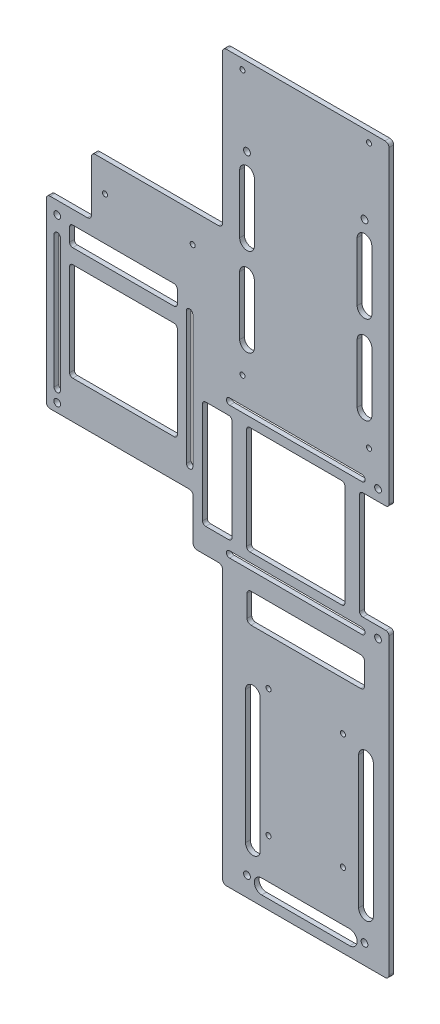
SolidWorks part; units mm, degrees
material "Acrylic (Medium-high impact)"
ref_plane "Front Plane" through (0, 0, 0) normal (0, 0, 1) x (1, 0, 0)
ref_plane "Top Plane" through (0, 0, 0) normal (0, 1, 0) x (1, 0, 0)
ref_plane "Right Plane" through (0, 0, 0) normal (1, 0, 0) x (0, 0, -1)
sketch "Sketch1" plane through (0, 0, 0) normal (0, 0, 1) x (1, 0, 0)
  line L1 (-159.4912, -174.7551) -> (-51.5412, -174.7551)
  line L2 (-159.4912, -174.7551) -> (-159.4912, 295.1449)
  line L3 (-159.4912, 295.1449) -> (-51.5412, 295.1449)
  line L4 (-51.5412, -174.7551) -> (-51.5412, 295.1449)
  line L5 (-159.4912, -174.7551) -> (-51.5412, 295.1449) construction
  line L6 (-159.4912, 295.1449) -> (-51.5412, -174.7551) construction
  point P0 (-105.5162, 60.1949)
  dimension "D1" = 107.95
  dimension "D2" = 469.9
extrude "Boss-Extrude1" add sketch "Sketch1" along normal blind 3.0734
sketch "Sketch2" plane through (0, 0, 3.0734) normal (0, 0, 1) x (1, 0, 0)
  line L0 (-134.0912, -163.6426) -> (-76.9412, -163.6426) construction
  line L1 (-134.0912, -158.8801) -> (-76.9412, -158.8801)
  line L2 (-134.0912, -168.4051) -> (-76.9412, -168.4051)
  line L3 (-105.5162, 295.1449) -> (-105.5162, -174.7551) construction
  line L4 (-159.4912, 295.1449) -> (-159.4912, -174.7551) construction
  line L5 (-51.5412, -174.7551) -> (-51.5412, 295.1449) construction
  line L6 (-51.5412, 295.1449) -> (-159.4912, 295.1449) construction
  line L7 (-159.4912, -174.7551) -> (-51.5412, -174.7551) construction
  line L8 (-66.4637, -58.2591) -> (-66.4637, -144.2751) construction
  line L9 (-61.7012, -58.2591) -> (-61.7012, -144.2751)
  line L10 (-71.2262, -58.2591) -> (-71.2262, -144.2751)
  line L11 (-139.8062, -58.2591) -> (-139.8062, -144.2751) construction
  line L13 (-68.7497, -58.2591) -> (-67.4797, -58.2591) construction
  line L14 (-144.5687, -58.2591) -> (-144.5687, -144.2751)
  line L15 (-135.0437, -58.2591) -> (-135.0437, -144.2751)
  line L16 (-139.8062, -144.2751) -> (-105.5162, -144.2751) construction
  line L17 (-105.5162, -144.2751) -> (-71.2262, -144.2751) construction
  arc A0 (-134.0912, -158.8801) -> (-134.0912, -168.4051) centre (-134.0912, -163.6426) ccw
  arc A1 (-76.9412, -168.4051) -> (-76.9412, -158.8801) centre (-76.9412, -163.6426) ccw
  arc A2 (-61.7012, -58.2591) -> (-71.2262, -58.2591) centre (-66.4637, -58.2591) ccw
  arc A3 (-71.2262, -144.2751) -> (-61.7012, -144.2751) centre (-66.4637, -144.2751) ccw
  arc A4 (-144.5687, -58.2591) -> (-135.0437, -58.2591) centre (-139.8062, -58.2591) cw
  arc A5 (-135.0437, -144.2751) -> (-144.5687, -144.2751) centre (-139.8062, -144.2751) cw
  point P2 (-105.5162, -163.6426)
  point P15 (-66.4637, -101.2671)
  point P30 (-139.8062, -101.2671)
  dimension "D1" = 6.35
  dimension "D2" = 25.4
  dimension "D3" = 25.4
  dimension "D4" = 10.16
  dimension "D5" = 0
  dimension "D6" = 9.525
  dimension "D7" = 30.48
  dimension "D8" = 9.525
extrude "Arudino Wire Slots" cut sketch "Sketch2" against normal up to next
sketch "Sketch6" plane through (0, 0, 3.0734) normal (0, 0, 1) x (1, 0, 0)
  line L3 (-51.5412, 295.1449) -> (-159.4912, 295.1449) construction
  line L4 (-51.5412, -174.7551) -> (-51.5412, 295.1449) construction
  line L13 (-67.4162, 231.6449) -> (-67.4162, 193.5449) construction
  line L14 (-62.6537, 231.6449) -> (-62.6537, 193.5449)
  line L15 (-72.1787, 231.6449) -> (-72.1787, 193.5449)
  arc A2 (-62.6537, 231.6449) -> (-72.1787, 231.6449) centre (-67.4162, 231.6449) ccw
  arc A3 (-72.1787, 193.5449) -> (-62.6537, 193.5449) centre (-67.4162, 193.5449) ccw
  point P23 (-67.4162, 212.5949)
  dimension "D1" = 15.875
  dimension "D2" = 63.5
  dimension "D3" = 9.525
  dimension "D4" = 38.1
extrude "PowerBoardWirePass" cut sketch "Sketch6" against normal up to next (3.0734 mm away)
pattern_linear "LPattern2" count 2 spacing 57.15 along (0, -1, 0) count 2 spacing 76.2 along (-1, 0, 0) of "PowerBoardWirePass"
sketch "Sketch8" plane through (0, 0, 3.0734) normal (0, 0, 1) x (1, 0, 0)
  line L0 (-159.4912, -10.8302) -> (-51.5412, -10.8302) construction
  line L1 (-159.4912, 295.1449) -> (-159.4912, -174.7551) construction
  line L2 (-51.5412, -174.7551) -> (-51.5412, 295.1449) construction
  line L4 (-143.6162, -20.3552) -> (-67.4162, -20.3552)
  line L5 (-143.6162, -20.3552) -> (-143.6162, -1.3052)
  line L6 (-143.6162, -1.3052) -> (-67.4162, -1.3052)
  line L7 (-67.4162, -20.3552) -> (-67.4162, -1.3052)
  line L8 (-143.6162, -20.3552) -> (-67.4162, -1.3052) construction
  line L9 (-143.6162, -1.3052) -> (-67.4162, -20.3552) construction
  point P6 (-105.5162, -10.8302)
  dimension "D1" = 19.05
  dimension "D2" = 76.2
extrude "Cut-Extrude5" cut sketch "Sketch8" against normal through all
hole_wizard "#30 (0.1285) Arduino Mounts" positions "Sketch14" profile "Sketch15" hole size "#30" standard "ANSI Inch" end condition through all
sketch "Sketch14" plane through (0, 0, 3.0734) normal (0, 0, 1) x (1, 0, 0)
  line L0 (-159.4912, -174.7551) -> (-51.5412, -174.7551) construction
  line L3 (-105.5162, -34.436) -> (-105.5162, -174.7551) construction
  point P0 (-129.6462, -50.2951)
  point P2 (-129.6462, -132.8451)
  point P4 (-81.3862, -51.5651)
  point P6 (-81.3862, -126.4951)
  dimension "D1" = 48.26
  dimension "D2" = 82.55
  dimension "D3" = 74.93
  dimension "D4" = 41.91
  dimension "D5" = 1.27
  dimension "D6" = 24.13
sketch "Sketch15" plane through (-129.6462, -50.2951, 3.0734) normal (1, 0, 0) x (0, -1, 0)
  line L0 (0, 0) -> (0, 3.0734)
  line L1 (0, 3.0734) -> (1.6319, 3.0734)
  line L2 (1.6319, 3.0734) -> (1.6319, 0)
  line L5 (1.6319, 0) -> (0, 0)
  line L11 (0, -6.35) -> (0, 107.95) construction
  dimension "Thru Hole Dia." = 3.2639
  dimension "Thru Hole Depth" = 3.0734
sketch "Sketch18" plane through (0, 0, 0) normal (0, 0, 1) x (1, 0, 0)
  line L0 (-159.4912, 193.5449) -> (-273.7912, 193.5449)
  line L1 (-159.4912, 295.1449) -> (-159.4912, -174.7551) construction
  line L2 (-273.7912, 193.5449) -> (-273.7912, 36.0649)
  line L3 (-273.7912, 36.0649) -> (-178.5412, 36.0649)
  line L4 (-159.4912, 193.5449) -> (-159.4912, 4.3149)
  line L5 (-51.5412, 295.1449) -> (-159.4912, 295.1449) construction
  line L6 (-178.5412, 36.0649) -> (-178.5412, 4.3149)
  line L7 (-178.5412, 4.3149) -> (-159.4912, 4.3149)
  line L8 (-159.4912, 295.1449) -> (-159.4912, -174.7551) construction
  dimension "D1" = 259.08
  dimension "D2" = 114.3
  dimension "D3" = 101.6
  dimension "D4" = 19.05
  dimension "D5" = 31.75
extrude "Boss-Extrude2" add sketch "Sketch18" along normal blind 3.0734
hole_wizard "#30 (0.1285) Diameter Hole1" positions "Sketch12" profile "Sketch13" hole size "#30" standard "ANSI Inch" end condition through all
sketch "Sketch12" plane through (0, 0, 3.0734) normal (0, 0, 1) x (1, 0, 0)
  line L0 (-146.5372, 117.3449) -> (-146.5372, 288.7949) construction
  line L1 (-146.5372, 288.7949) -> (-64.4952, 288.7949) construction
  line L2 (-64.4952, 288.7949) -> (-64.4952, 117.3449) construction
  line L3 (-64.4952, 117.3449) -> (-146.5372, 117.3449) construction
  line L5 (-51.5412, 295.1449) -> (-159.4912, 295.1449) construction
  line L7 (-105.5162, 295.1449) -> (-105.5162, 288.7949) construction
  line L8 (-159.4912, 193.5449) -> (-273.7912, 193.5449) construction
  line L9 (-273.7912, 193.5449) -> (-273.7912, 36.0649) construction
  point P0 (-64.4952, 288.7949)
  point P2 (-146.5372, 288.7949)
  point P4 (-146.5372, 117.3449)
  point P6 (-64.4952, 117.3449)
  point P26 (-235.6912, 174.4949)
  point P28 (-178.8714, 174.4949)
  dimension "D1" = 82.042
  dimension "D2" = 171.45
  dimension "D3" = 6.35
  dimension "D4" = 19.05
  dimension "D5" = 38.1
  dimension "D6" = 56.8198
sketch "Sketch13" plane through (-64.4952, 288.7949, 3.0734) normal (1, 0, 0) x (0, -1, 0)
  line L0 (0, 0) -> (0, 3.0734)
  line L1 (0, 3.0734) -> (1.6319, 3.0734)
  line L2 (1.6319, 3.0734) -> (1.6319, 0)
  line L5 (1.6319, 0) -> (0, 0)
  line L11 (0, -6.35) -> (0, 107.95) construction
  dimension "Thru Hole Dia." = 3.2639
  dimension "Thru Hole Depth" = 3.0734
sketch "Sketch19" plane through (0, 0, 3.0734) normal (0, 0, 1) x (1, 0, 0)
  line L0 (-153.3952, 88.2386) -> (-153.3952, 22.4886)
  line L1 (-162.9202, 75.7358) -> (-162.9202, 39.7972) construction
  line L2 (-172.4452, 88.2386) -> (-172.4452, 22.4886)
  line L3 (-170.3952, 90.2886) -> (-155.4452, 90.2886)
  line L4 (-426.1023, 140.2049) -> (-409.9638, 140.2049) construction
  line L5 (-256.6409, 146.5549) -> (-190.8909, 146.5549)
  line L6 (-170.3952, 20.4386) -> (-155.4452, 20.4386)
  line L7 (-223.7659, 60.5759) -> (-223.7659, 124.3299) construction
  line L9 (-51.5412, 295.1449) -> (-159.4912, 295.1449) construction
  line L12 (-266.6972, 49.5269) -> (-266.6972, 135.3789) construction
  line L13 (-268.7472, 49.5269) -> (-268.7472, 135.3789)
  line L14 (-51.5412, -174.7551) -> (-51.5412, 295.1449) construction
  line L15 (-154.9192, 98.2949) -> (-69.0672, 98.2949) construction
  line L16 (-154.9192, 100.3449) -> (-69.0672, 100.3449)
  line L17 (-154.9192, 96.2449) -> (-69.0672, 96.2449)
  line L18 (-53.5912, 90.2886) -> (-68.5412, 90.2886)
  line L19 (-70.5912, 88.2386) -> (-70.5912, 22.4886)
  line L20 (-68.5412, 20.4386) -> (-53.5912, 20.4386)
  line L21 (-51.5412, 92.3386) -> (-51.5412, 18.3886)
  line L22 (-264.6472, 49.5269) -> (-264.6472, 135.3789)
  line L23 (-154.3518, 55.3689) -> (-93.9593, 55.3689) construction
  line L24 (-154.9192, 12.4429) -> (-69.0672, 12.4429) construction
  line L25 (-154.9192, 10.3929) -> (-69.0672, 10.3929)
  line L26 (-154.9192, 14.4929) -> (-69.0672, 14.4929)
  line L27 (-75.3537, 88.6756) -> (-75.3537, 77.0683) construction
  line L28 (-80.1162, 88.2386) -> (-80.1162, 22.4886)
  line L29 (-111.9932, 87.7921) -> (-111.9932, 31.1048) construction
  line L30 (-143.8702, 88.2386) -> (-143.8702, 22.4886)
  line L31 (-141.8202, 90.2886) -> (-82.1662, 90.2886)
  line L32 (-258.6909, 135.9049) -> (-258.6909, 144.5049)
  line L33 (-82.1662, 20.4386) -> (-141.8202, 20.4386)
  line L34 (-256.6409, 133.8549) -> (-190.8909, 133.8549)
  line L35 (-188.8409, 135.9049) -> (-188.8409, 144.5049)
  line L38 (-180.8452, 49.5269) -> (-180.8452, 135.3789) construction
  line L39 (-178.7952, 49.5269) -> (-178.7952, 135.3789)
  line L40 (-182.8952, 49.5269) -> (-182.8952, 135.3789)
  line L41 (-454.9809, 129.0924) -> (-443.3736, 129.0924) construction
  line L42 (-256.6409, 124.3299) -> (-190.8909, 124.3299)
  line L43 (-258.6909, 92.4529) -> (-188.8515, 92.4529) construction
  line L44 (-256.6409, 60.5759) -> (-190.8909, 60.5759)
  line L45 (-258.6909, 62.6259) -> (-258.6909, 122.2799)
  line L46 (-188.8409, 122.2799) -> (-188.8409, 62.6259)
  arc A0 (-51.5412, 92.3386) -> (-53.5912, 90.2886) centre (-53.5912, 92.3386) cw
  arc A1 (-154.9192, 100.3449) -> (-154.9192, 96.2449) centre (-154.9192, 98.2949) ccw
  arc A2 (-69.0672, 96.2449) -> (-69.0672, 100.3449) centre (-69.0672, 98.2949) ccw
  arc A3 (-53.5912, 20.4386) -> (-51.5412, 18.3886) centre (-53.5912, 18.3886) cw
  arc A4 (-68.5412, 90.2886) -> (-70.5912, 88.2386) centre (-68.5412, 88.2386) ccw
  arc A5 (-70.5912, 22.4886) -> (-68.5412, 20.4386) centre (-68.5412, 22.4886) ccw
  circle A6 centre (-64.4952, 117.3449) radius 1.6319 construction
  arc A7 (-154.9192, 10.3929) -> (-154.9192, 14.4929) centre (-154.9192, 12.4429) cw
  arc A8 (-69.0672, 14.4929) -> (-69.0672, 10.3929) centre (-69.0672, 12.4429) cw
  arc A9 (-80.1162, 22.4886) -> (-82.1662, 20.4386) centre (-82.1662, 22.4886) cw
  arc A10 (-82.1662, 90.2886) -> (-80.1162, 88.2386) centre (-82.1662, 88.2386) cw
  arc A11 (-143.8702, 22.4886) -> (-141.8202, 20.4386) centre (-141.8202, 22.4886) ccw
  arc A12 (-141.8202, 90.2886) -> (-143.8702, 88.2386) centre (-141.8202, 88.2386) ccw
  arc A13 (-153.3952, 22.4886) -> (-155.4452, 20.4386) centre (-155.4452, 22.4886) cw
  arc A14 (-155.4452, 90.2886) -> (-153.3952, 88.2386) centre (-155.4452, 88.2386) cw
  arc A15 (-172.4452, 22.4886) -> (-170.3952, 20.4386) centre (-170.3952, 22.4886) ccw
  arc A16 (-170.3952, 90.2886) -> (-172.4452, 88.2386) centre (-170.3952, 88.2386) ccw
  arc A18 (-268.7472, 49.5269) -> (-264.6472, 49.5269) centre (-266.6972, 49.5269) ccw
  arc A19 (-264.6472, 135.3789) -> (-268.7472, 135.3789) centre (-266.6972, 135.3789) ccw
  arc A21 (-258.6909, 135.9049) -> (-256.6409, 133.8549) centre (-256.6409, 135.9049) ccw
  arc A22 (-190.8909, 133.8549) -> (-188.8409, 135.9049) centre (-190.8909, 135.9049) ccw
  arc A23 (-178.7952, 49.5269) -> (-182.8952, 49.5269) centre (-180.8452, 49.5269) cw
  arc A24 (-182.8952, 135.3789) -> (-178.7952, 135.3789) centre (-180.8452, 135.3789) cw
  arc A25 (-190.8909, 124.3299) -> (-188.8409, 122.2799) centre (-190.8909, 122.2799) cw
  arc A26 (-258.6909, 122.2799) -> (-256.6409, 124.3299) centre (-256.6409, 122.2799) cw
  arc A27 (-190.8909, 60.5759) -> (-188.8409, 62.6259) centre (-190.8909, 62.6259) ccw
  arc A28 (-258.6909, 62.6259) -> (-256.6409, 60.5759) centre (-256.6409, 62.6259) ccw
  arc A33 (-190.8909, 146.5549) -> (-188.8409, 144.5049) centre (-190.8909, 144.5049) cw
  arc A34 (-258.6909, 144.5049) -> (-256.6409, 146.5549) centre (-256.6409, 144.5049) cw
  point P19 (-111.9932, 98.2949)
  point P41 (-111.9932, 12.4429)
  point P79 (-266.6972, 92.4529)
  point P97 (-180.8452, 92.4529)
  point P121 (-258.6909, 92.4529)
  dimension "D8" = 19.05
  dimension "D9" = 4.1
  dimension "D2" = 9.525
  dimension "D3" = 6.35
  dimension "D4" = 4.1
  dimension "D5" = 85.852
  dimension "D6" = 69.85
  dimension "D7" = 85.852
  dimension "D10" = 19.05
  dimension "D11" = 85.852
  dimension "D12" = 69.85
  dimension "D13" = 5.9563
  dimension "D14" = 42.926
  dimension "D15" = 4.7625
  dimension "D16" = 31.877
  dimension "D17" = 4.572
  dimension "D18" = 42.9313
  dimension "D19" = 4.7625
  dimension "D20" = 31.877
  dimension "D21" = 148.59
  dimension "D22" = 6.35
extrude "Cut-Extrude6" cut sketch "Sketch19" against normal through all
fillet "Fillet1" radius 2.54 4 edges at (-67.4162, -1.3052, 1.5367) (-143.6162, -1.3052, 1.5367) (-143.6162, -20.3552, 1.5367) (-67.4162, -20.3552, 1.5367)
fillet "Fillet3" radius 2.54 5 edges at (-159.4912, 193.5449, 1.5367) (-159.4912, 4.3149, 1.5367) (-178.5412, 4.3149, 1.5367) (-178.5412, 36.0649, 1.5367) (-273.7912, 36.0649, 1.5367)
sketch "Sketch7" plane through (0, 0, 3.0734) normal (0, 0, 1) x (1, 0, 0)
  line L0 (-159.4912, -174.7551) -> (-51.5412, -174.7551) construction
  line L1 (-67.4162, -162.0551) -> (-51.5412, -162.0551) construction
  line L2 (-67.4162, -162.0551) -> (-143.6162, -162.0551) construction
  line L3 (-67.4162, -162.0551) -> (-67.4162, 244.3449) construction
  line L4 (-67.4162, 244.3449) -> (-143.6162, 244.3449) construction
  line L5 (-143.6162, -162.0551) -> (-143.6162, 244.3449) construction
  line L6 (-67.4162, -162.0551) -> (-143.6162, 244.3449) construction
  line L7 (-67.4162, 244.3449) -> (-143.6162, -162.0551) construction
  line L8 (-51.5412, -174.7551) -> (-51.5412, 18.3886) construction
  line L9 (-143.6162, -162.0551) -> (-159.4912, -162.0551) construction
  line L10 (-159.4912, 295.1449) -> (-159.4912, 196.0849) construction
  line L11 (-266.6972, 147.1899) -> (-266.6972, 41.7799) construction
  line L12 (-271.2512, 36.0649) -> (-181.0812, 36.0649) construction
  line L14 (-51.5412, 92.3386) -> (-51.5412, 295.1449) construction
  line L15 (-53.5912, 90.2886) -> (-68.5412, 90.2886) construction
  line L16 (-68.5412, 20.4386) -> (-53.5912, 20.4386) construction
  circle A0 centre (-143.6162, 244.3449) radius 2.1971
  circle A1 centre (-67.4162, 244.3449) radius 2.1971
  circle A2 centre (-143.6162, -162.0551) radius 2.1971
  circle A3 centre (-67.4162, -162.0551) radius 2.1971
  circle A4 centre (-266.6972, 147.1899) radius 2.1971
  circle A5 centre (-266.6972, 41.7799) radius 2.1971
  circle A6 centre (-58.6532, 97.4006) radius 2.1971
  circle A7 centre (-58.6532, 13.3266) radius 2.1971
  point P33 (0, 0)
  dimension "D3" = 4.3942
  dimension "D4" = 12.7
  dimension "D5" = 105.41
  dimension "D6" = 5.715
  dimension "D1" = 76.2
  dimension "D2" = 406.4
  dimension "D7" = 7.112
  dimension "D8" = 7.112
  dimension "D9" = 7.112
extrude "Brain-Panel-Mounts" cut sketch "Sketch7" against normal through all
sketch "Sketch21" plane through (0, 0, 3.0734) normal (0, 0, 1) x (1, 0, 0)
  line L0 (-273.7912, 193.5449) -> (-273.7912, 155.4449)
  line L1 (-273.7912, 193.5449) -> (-273.7912, 38.6049) construction
  line L2 (-273.7912, 155.4449) -> (-244.5812, 155.4449)
  line L3 (-244.5812, 155.4449) -> (-244.5812, 193.5449)
  line L4 (-162.0312, 193.5449) -> (-273.7912, 193.5449) construction
  line L5 (-273.7912, 193.5449) -> (-244.5812, 193.5449)
  dimension "D1" = 38.1
  dimension "D2" = 29.21
extrude "Cut-Extrude7" cut sketch "Sketch21" against normal through all
fillet "Fillet2" radius 2.54 7 edges at (-159.4912, 295.1449, 1.5367) (-51.5412, 295.1449, 1.5367) (-51.5412, -174.7551, 1.5367) (-159.4912, -174.7551, 1.5367) (-244.5812, 193.5449, 1.5367) (-273.7912, 155.4449, 1.5367) (-244.5812, 155.4449, 1.5367)
